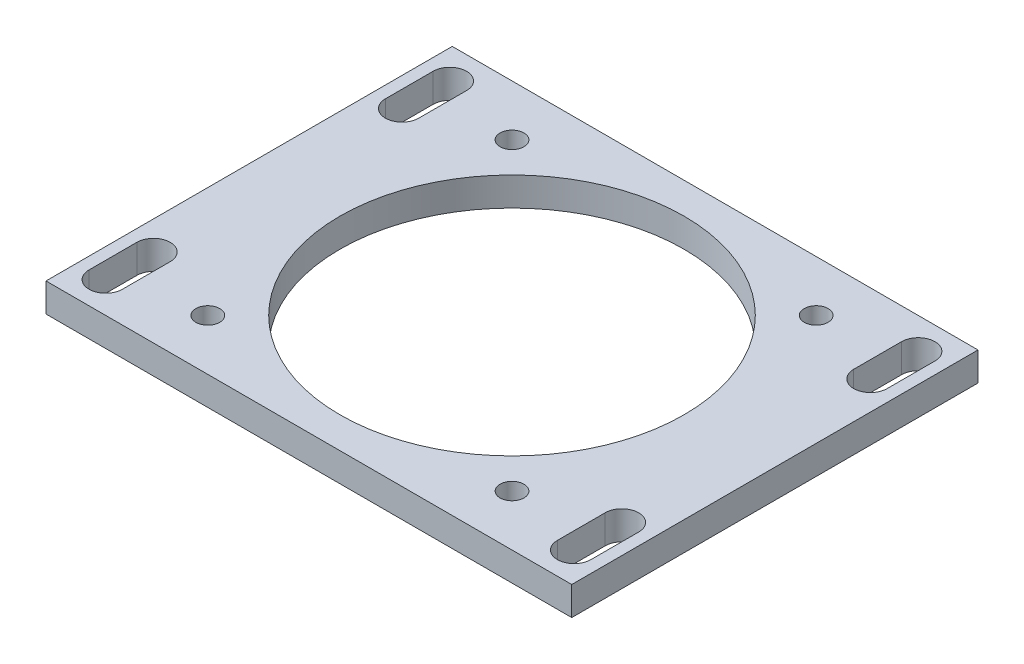
SolidWorks part; units mm, degrees
ref_plane "前视基准面" through (0, 0, 0) normal (0, 0, 1) x (1, 0, 0)
ref_plane "上视基准面" through (0, 0, 0) normal (0, 1, 0) x (1, 0, 0)
ref_plane "右视基准面" through (0, 0, 0) normal (1, 0, 0) x (0, 0, -1)
sketch "草图1" plane through (0, 0, 0) normal (0, 1, 0) x (1, 0, 0)
  line L1 (-55, 42.5) -> (55, 42.5)
  line L2 (-55, 42.5) -> (-55, -42.5)
  line L3 (-55, -42.5) -> (55, -42.5)
  line L4 (55, 42.5) -> (55, -42.5)
  line L5 (-55, 42.5) -> (55, -42.5) construction
  line L6 (-55, -42.5) -> (55, 42.5) construction
  point P0 (0, 0)
  dimension "D1" = 110
  dimension "D2" = 85
extrude "凸台-拉伸1" add sketch "草图1" along normal blind 6
sketch "草图2" plane through (0, 6, 0) normal (0, 1, 0) x (1, 0, 0)
  circle A0 centre (0, 0) radius 36
  dimension "D1" = 72
extrude "切除-拉伸1" cut sketch "草图2" against normal blind 10
sketch "草图3" plane through (0, 6, 0) normal (0, 1, 0) x (1, 0, 0)
  line L0 (-49, 36) -> (-49, 26) construction
  line L1 (-45.5, 36) -> (-45.5, 26)
  line L2 (-52.5, 36) -> (-52.5, 26)
  line L3 (55, 42.5) -> (-55, 42.5) construction
  line L4 (0, 0) -> (59.2454, 0) construction
  line L5 (0, 0) -> (0, -25.9199) construction
  line L6 (49, 36) -> (49, 26) construction
  line L7 (45.5, 36) -> (45.5, 26)
  line L8 (52.5, 36) -> (52.5, 26)
  line L9 (-49, -36) -> (-49, -26) construction
  line L10 (-45.5, -36) -> (-45.5, -26)
  line L11 (-52.5, -36) -> (-52.5, -26)
  line L12 (49, -36) -> (49, -26) construction
  line L13 (45.5, -36) -> (45.5, -26)
  line L14 (52.5, -36) -> (52.5, -26)
  arc A0 (-45.5, 36) -> (-52.5, 36) centre (-49, 36) ccw
  arc A1 (-52.5, 26) -> (-45.5, 26) centre (-49, 26) ccw
  arc A2 (45.5, 36) -> (52.5, 36) centre (49, 36) cw
  arc A3 (52.5, 26) -> (45.5, 26) centre (49, 26) cw
  arc A4 (-45.5, -36) -> (-52.5, -36) centre (-49, -36) cw
  arc A5 (-52.5, -26) -> (-45.5, -26) centre (-49, -26) cw
  arc A6 (45.5, -36) -> (52.5, -36) centre (49, -36) ccw
  arc A7 (52.5, -26) -> (45.5, -26) centre (49, -26) ccw
  point P2 (-49, 31)
  point P15 (49, 31)
  point P22 (-49, -31)
  point P29 (49, -31)
  dimension "D4" = 3.5
  dimension "D1" = 10
  dimension "D2" = 6.5
  dimension "D3" = 49
  dimension "D5" = 98
  dimension "D6" = 42.5
extrude "切除-拉伸2" cut sketch "草图3" against normal blind 10
sketch "草图4" plane through (0, 6, 0) normal (0, 1, 0) x (1, 0, 0)
  line L0 (-31.8198, 31.8198) -> (31.8198, 31.8198) construction
  circle A0 centre (0, 0) radius 45 construction
  point P3 (31.8198, -31.8198)
  point P4 (31.8198, 31.8198)
  point P5 (-31.8198, 31.8198)
  point P6 (-31.8198, -31.8198)
  dimension "D1" = 90
hole_wizard "M6 螺纹孔1" positions "3D草图1" profile "草图5" tap size "M6" standard "GB"
sketch3d "3D草图1"
  point P0 (-31.8198, 6, -31.8198)
  point P3 (31.8198, 6, -31.8198)
  point P6 (31.8198, 6, 31.8198)
  point P9 (-31.8198, 6, 31.8198)
sketch "草图5" plane through (-31.8198, 6, -31.8198) normal (1, 0, 0) x (0, 0, 1)
  line L0 (0, 0) -> (0, 16.5022)
  line L1 (0, 16.5022) -> (2.5, 15)
  line L2 (2.5, 15) -> (2.5, 0)
  line L5 (2.5, 0) -> (0, 0)
  line L10 (0, 16.5022) -> (-2.5, 15) construction
  line L11 (0, -6.35) -> (0, 107.95) construction
  dimension "螺纹孔钻头直径" = 5
  dimension "螺纹孔钻头深度" = 15
  dimension "导头角度" = 118
cosmetic thread "孔螺蚊线1" parameters "D1"=5, "D2"=6
cosmetic thread "孔螺蚊线2" parameters "D1"=5, "D2"=6
cosmetic thread "孔螺蚊线3" parameters "D1"=5, "D2"=6
cosmetic thread "孔螺蚊线4" parameters "D1"=5, "D2"=6
